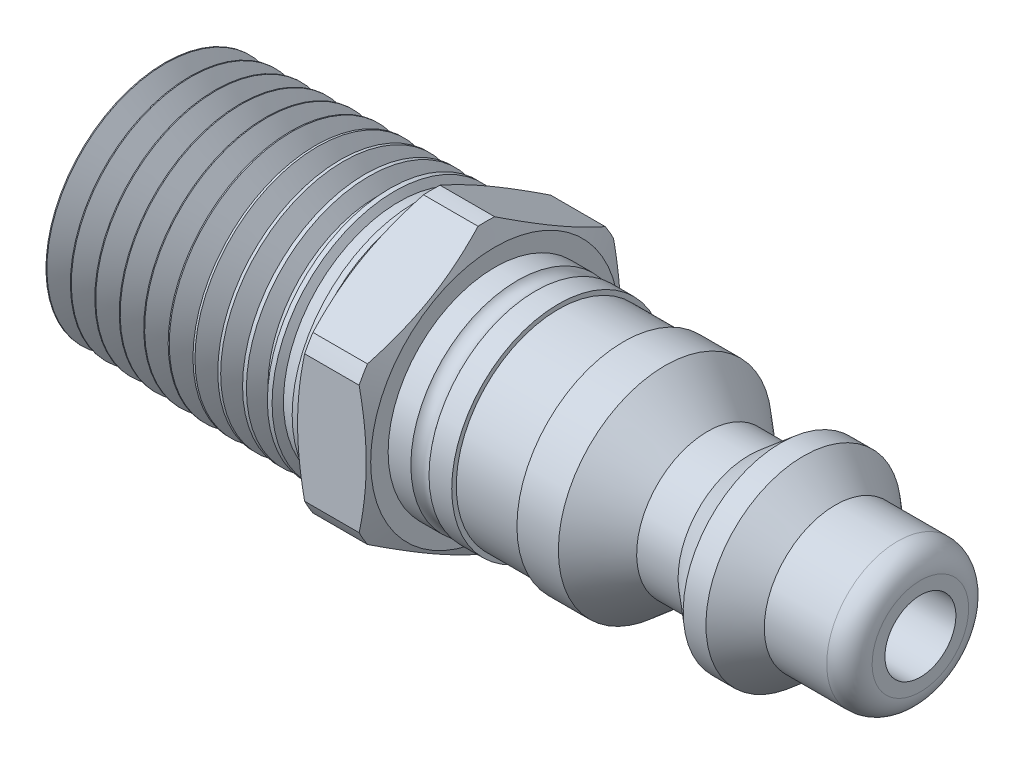
SolidWorks part; units mm, degrees
ref_plane "Front" through (0, 0, 0) normal (0, 0, 1) x (1, 0, 0)
ref_plane "Top" through (0, 0, 0) normal (0, 1, 0) x (1, 0, 0)
ref_plane "Right" through (0, 0, 0) normal (1, 0, 0) x (0, 0, -1)
sketch "Sketch1" plane through (0, 0, 0) normal (0, 0, 1) x (1, 0, 0)
  line L0 (0, 0) -> (0, 5.4466)
  line L1 (0, 5.4466) -> (0.667, 6.6901) construction
  line L2 (0.667, 6.6901) -> (1.4104, 5.4907) construction
  line L3 (1.4104, 5.4907) -> (2.0775, 6.7342) construction
  line L4 (2.0775, 6.7342) -> (2.8208, 5.5347) construction
  line L5 (1.4359, 5.5381) -> (2.052, 6.6867)
  line L6 (2.052, 6.6867) -> (2.1058, 6.6884)
  line L7 (2.1058, 6.6884) -> (2.7925, 5.5805)
  line L8 (2.7925, 5.5805) -> (2.8463, 5.5821)
  line L9 (0, 5.4466) -> (2.8208, 5.5347) construction
  line L10 (0.667, 6.6901) -> (2.0775, 6.7342) construction
  line L11 (0.3335, 6.0683) -> (2.4492, 6.1344) construction
  line L12 (0, 0) -> (-5.4466, 0) construction
  line L13 (2.8463, 5.5821) -> (3.4625, 6.7308)
  line L14 (0.0254, 5.494) -> (0.6416, 6.6427)
  line L15 (0.6416, 6.6427) -> (0.6954, 6.6443)
  line L16 (0.6954, 6.6443) -> (1.3821, 5.5364)
  line L17 (1.3821, 5.5364) -> (1.4359, 5.5381)
  line L18 (0.3335, 6.0683) -> (0, 6.0579) construction
  line L19 (0, 6.0579) -> (0, 5.4466) construction
  line L20 (0.3335, -6.0683) -> (0, -6.0579) construction
  line L21 (0.0254, 5.494) -> (0, 5.4466)
  line L22 (3.4625, 6.7308) -> (3.5162, 6.7325)
  line L23 (3.5162, 6.7325) -> (4.2029, 5.6245)
  line L24 (4.2029, 5.6245) -> (4.2567, 5.6262)
  line L25 (4.2567, 5.6262) -> (4.8729, 6.7749)
  line L26 (4.8729, 6.7749) -> (4.9266, 6.7766)
  line L27 (4.9266, 6.7766) -> (5.6133, 5.6686)
  line L28 (5.6133, 5.6686) -> (5.6671, 5.6703)
  line L29 (5.6671, 5.6703) -> (6.2833, 6.819)
  line L30 (6.2833, 6.819) -> (6.3371, 6.8207)
  line L31 (6.3371, 6.8207) -> (7.0238, 5.7127)
  line L32 (7.0238, 5.7127) -> (7.0775, 5.7144)
  line L33 (7.0775, 5.7144) -> (7.6937, 6.8631)
  line L34 (7.6937, 6.8631) -> (7.7475, 6.8647)
  line L35 (7.7475, 6.8647) -> (8.4342, 5.7568)
  line L36 (8.4342, 5.7568) -> (8.488, 5.7584)
  line L37 (8.488, 5.7584) -> (9.1041, 6.9071)
  line L38 (9.1041, 6.9071) -> (9.1579, 6.9088)
  line L39 (9.1579, 6.9088) -> (9.8446, 5.8008)
  line L40 (9.8446, 5.8008) -> (9.8984, 5.8025)
  line L41 (9.8984, 5.8025) -> (10.5146, 6.9512)
  line L42 (10.5146, 6.9512) -> (10.5683, 6.9529)
  line L43 (10.5683, 6.9529) -> (11.255, 5.8449)
  line L44 (11.255, 5.8449) -> (11.3088, 5.8466)
  line L45 (11.3088, 5.8466) -> (11.925, 6.9953)
  line L46 (11.925, 6.9953) -> (11.9788, 6.997)
  line L47 (11.9788, 6.997) -> (12.6655, 5.889)
  line L48 (12.6655, 5.889) -> (12.7192, 5.8907)
  line L49 (12.7192, 5.8907) -> (13.3354, 7.0394)
  line L50 (13.3354, 7.0394) -> (13.3892, 7.041)
  line L51 (13.3892, 7.041) -> (14.0759, 5.9331)
  line L52 (14.0759, 5.9331) -> (14.1297, 5.9348)
  line L53 (14.1297, 5.9348) -> (14.7458, 7.0834)
  line L54 (14.7458, 7.0834) -> (14.7996, 7.0851)
  line L55 (14.7996, 7.0851) -> (15.4863, 5.9772)
  line L56 (15.4863, 5.9772) -> (15.5401, 5.9788)
  line L57 (15.5401, 5.9788) -> (16.1563, 7.1275)
  line L58 (16.1563, 7.1275) -> (16.21, 7.1292)
  line L59 (16.21, 7.1292) -> (16.8967, 6.0212)
  line L60 (16.8967, 6.0212) -> (16.9505, 6.0229)
  line L61 (0, 0) -> (42.9, 0) construction
  line L62 (0, 4.6228) -> (0, -4.6228) construction
  line L73 (0, 0) -> (16.9505, 0)
  line L74 (16.9505, 0) -> (16.9505, 6.0229)
  line L75 (0.6685, 6.6435) -> (0.667, 6.6901) construction
  line L76 (2.4492, 6.1344) -> (10.2108, 6.377) construction
  line L77 (10.2108, 6.377) -> (10.2108, 0) construction
  line L78 (10.2108, 6.377) -> (15.1028, 6.5299) construction
  line L79 (15.1028, 6.5299) -> (15.1028, 0) construction
  line L80 (15.1028, 6.5299) -> (15.1028, 6.858) construction
  line L81 (15.1028, 6.858) -> (16.9505, 6.858) construction
  line L82 (16.9505, 6.858) -> (16.9505, 6.0229) construction
  line L84 (10.2108, 5.8123) -> (15.1028, 5.9652) construction
  line L87 (15.1028, 5.4466) -> (0, 5.4466) construction
  point P75 (19.1002, 0)
  dimension "D1" = 60
  dimension "E0" = 12.1158
  dimension "Thread Pitch" = 1.4111
  dimension "D4" = 3.58
  dimension "D2" = 0.0466
  dimension "D3" = 0.0538
  dimension "L2 Thread Engagement" = 10.2108
  dimension "L4 Thread Length" = 15.1028
  dimension "Pipe OD" = 13.716
  dimension "Length" = 42.9
  dimension "ID" = 9.2456
  dimension "Plug End" = 23.7998
revolve "Revolve1" add sketch "Sketch1" angle 360 about L12
sketch "Sketch5" plane through (0, 0, 0) normal (0, 0, 1) x (1, 0, 0)
  line L0 (15.1028, 0) -> (15.1028, 7.0946)
  line L1 (15.1028, 7.0946) -> (16.9505, 7.1523)
  line L2 (16.9505, 7.1523) -> (16.9505, 0)
  line L3 (16.9505, 0) -> (15.1028, 0)
  line L4 (0, 0) -> (-5.4466, 0) construction
  line L5 (0, 0) -> (-5.4466, 0) construction
  line L6 (15.1028, 6.5299) -> (15.1028, 0) construction
  line L8 (16.1563, 7.1275) -> (16.21, 7.1292) construction
  line L9 (16.9505, 6.858) -> (16.9505, 6.0229) construction
  line L16 (0, 0) -> (42.9, 0) construction
revolve "Cut-Revolve2" cut sketch "Sketch5" angle 360 about L5
sketch "Sketch6" plane through (0, 0, 0) normal (0, 0, 1) x (1, 0, 0)
  line L0 (0, 0) -> (0, 5.4466) construction
  line L1 (16.9505, 6.858) -> (0, 6.858)
  line L2 (16.9505, 6.858) -> (16.9505, 20.6399)
  line L3 (16.9505, 20.6399) -> (0, 20.6399)
  line L4 (0, 6.858) -> (0, 20.6399)
revolve "Cut-Revolve3" cut sketch "Sketch6" angle 360 about L61
sketch "Sketch7" plane through (0, 0, 0) normal (0, 0, 1) x (1, 0, 0)
  line L0 (10.2108, 5.4466) -> (15.1028, 6.858)
  line L1 (10.2108, 6.377) -> (10.2108, 0) construction
  line L2 (15.1028, 5.4466) -> (0, 5.4466) construction
  line L3 (15.1028, 6.858) -> (15.1028, 5.4466)
  line L4 (15.1028, 5.4466) -> (10.2108, 5.4466)
revolve "Revolve2" add sketch "Sketch7" angle 360 about L61
sketch "Sketch8" plane through (15.1028, 0, 0) normal (1, 0, 0) x (0, 0, -1)
  line L1 (0, 8.2122) -> (-7.112, 4.1061)
  line L2 (-7.112, 4.1061) -> (-7.112, -4.1061)
  line L3 (-7.112, -4.1061) -> (0, -8.2122)
  line L4 (0, -8.2122) -> (7.112, -4.1061)
  line L5 (7.112, -4.1061) -> (7.112, 4.1061)
  line L6 (7.112, 4.1061) -> (0, 8.2122)
  circle A0 centre (0, 0) radius 7.112 construction
  dimension "Hex" = 14.224
extrude "Extrude1" add sketch "Sketch8" along normal up to vertex (3.9974 mm away) up to point (19.1002, 0, 0)
sketch "Sketch9" plane through (0, 0, 0) normal (0, 0, 1) x (1, 0, 0)
  line L0 (19.1002, 6.9422) -> (18.6264, 7.9582)
  line L1 (19.1002, 4.1061) -> (19.1002, 8.2122) construction
  line L2 (18.6264, 7.9582) -> (15.5766, 7.9582)
  line L3 (15.5766, 7.9582) -> (15.1028, 6.9422)
  line L4 (15.1028, 4.1061) -> (15.1028, 8.2122) construction
  line L5 (15.1028, 6.9422) -> (15.1028, 8.2122)
  line L6 (15.1028, 8.2122) -> (19.1002, 8.2122)
  line L7 (19.1002, 8.2122) -> (19.1002, 6.9422)
  dimension "D1" = 25
  dimension "D2" = 0.254
  dimension "D3" = 1.27
revolve "Cut-Revolve4" cut sketch "Sketch9" angle 360 about L61
sketch "Sketch10" plane through (0, 0, 0) normal (0, 0, 1) x (1, 0, 0)
  line L0 (19.1002, 0) -> (42.9, 0)
  line L1 (42.9, 0) -> (42.9, 3.9688)
  line L2 (42.9, 3.9688) -> (38.1375, 3.9688)
  line L3 (38.1375, 3.9688) -> (36.3624, 5.4582)
  line L4 (36.3624, 5.4582) -> (35.0924, 5.4582)
  line L5 (35.0924, 5.4582) -> (33.3173, 3.9688)
  line L6 (33.3173, 3.9688) -> (31.0001, 3.9688)
  line L7 (31.0001, 3.9688) -> (28.6196, 5.9662)
  line L8 (28.6196, 5.9662) -> (26.3024, 5.9662)
  line L9 (19.1002, -6.9422) -> (19.1002, 6.9422) construction
  line L10 (19.1002, 5.9662) -> (19.1002, 0)
  line L11 (42.9, 3.9688) -> (42.9, -3.9688) construction
  line L12 (26.3024, 5.9662) -> (26.3024, 5.7122)
  line L13 (26.3024, 5.7122) -> (22.6562, 5.7122)
  line L14 (22.6562, 5.7122) -> (22.6562, 5.9662)
  line L15 (22.6562, 5.9662) -> (21.3862, 5.9662)
  line L16 (20.3702, 5.9662) -> (19.1002, 5.9662)
  line L17 (22.6562, 5.7122) -> (20.8782, 5.7122) construction
  line L18 (28.6196, 5.9662) -> (35.7274, 5.9662) construction
  line L19 (35.7274, 5.9662) -> (35.7274, 5.4582) construction
  line L20 (31.0001, 3.9688) -> (31.0001, 0) construction
  arc A0 (21.3862, 5.9662) -> (20.3702, 5.9662) centre (20.8782, 6.3472) cw
  point P25 (35.7274, 5.7122)
  dimension "D3" = 100
  dimension "D4" = 0.635
  dimension "D1" = 0.254
  dimension "A" = 7.9375
  dimension "B" = 4.7625
  dimension "D2" = 1.27
revolve "Revolve3" add sketch "Sketch10" angle 360 about L12
fillet "Fillet1" radius 1.27 1 edges at (42.9, 3.9688, 0)
sketch "Sketch11" plane through (0, 0, 0) normal (0, 0, 1) x (1, 0, 0)
  line L0 (15.1028, 4.6228) -> (19.1002, 1.9844)
  line L1 (0, 4.6228) -> (15.1028, 4.6228)
  line L2 (0, 4.6228) -> (0, 0)
  line L3 (0, 0) -> (10.2108, 0)
  line L4 (19.1002, 1.9844) -> (42.9, 1.9844)
  line L5 (15.1028, 6.5299) -> (15.1028, 0) construction
  line L6 (42.9, 0) -> (42.9, 3.9688) construction
  line L8 (42.9, 1.9844) -> (42.9, 0)
  line L9 (42.9, 0) -> (10.2108, 0)
  line L12 (19.1002, 5.9662) -> (19.1002, 0) construction
  point P6 (0, 2.3114)
revolve "Cut-Revolve5" cut sketch "Sketch11" angle 360 about L12
equation "\"D2@Sketch1\"=\"Thread Pitch@Sketch1\"*.033"
